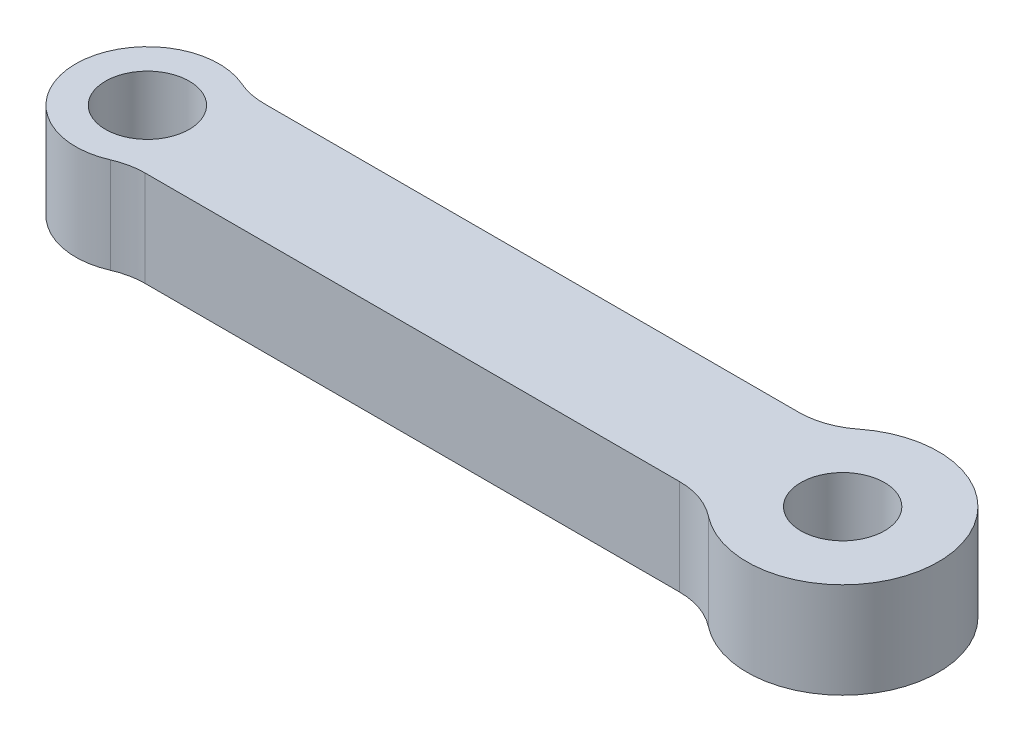
SolidWorks part; units mm, degrees
ref_plane "Ön Düzlem" through (0, 0, 0) normal (0, 0, 1) x (1, 0, 0)
ref_plane "Üst Düzlem" through (0, 0, 0) normal (0, 1, 0) x (1, 0, 0)
ref_plane "Sağ Düzlem" through (0, 0, 0) normal (1, 0, 0) x (0, 0, -1)
sketch "Çizim1" plane through (0, 0, 0) normal (0, 1, 0) x (1, 0, 0)
  line L0 (-55, 0) -> (55, 0) construction
  line L1 (-10.2187, -2.5) -> (4.0711, -2.5)
  line L2 (-10.2187, 2.5) -> (4.0711, 2.5)
  line L3 (-10.2187, 2.5) -> (-11.17, 2.5)
  line L4 (-10.2187, -2.5) -> (-11.17, -2.5)
  line L5 (4.0711, -2.5) -> (11.17, -2.5)
  line L6 (4.0711, 2.5) -> (11.17, 2.5)
  line L7 (0, -55) -> (0, 55) construction
  circle A0 centre (-13.5679, 0) radius 1.75
  arc A1 (-12.369, 2.75) -> (-12.369, -2.75) centre (-13.5679, 0) ccw
  circle A2 centre (15.5001, 0) radius 1.75
  arc A3 (13.0258, -3.1429) -> (13.0258, 3.1429) centre (15.5001, 0) ccw
  arc A4 (11.17, -2.5) -> (13.0258, -3.1429) centre (11.17, -5.5) cw
  arc A5 (11.17, 2.5) -> (13.0258, 3.1429) centre (11.17, 5.5) ccw
  arc A6 (-12.369, -2.75) -> (-11.17, -2.5) centre (-11.17, -5.5) cw
  arc A7 (-11.17, 2.5) -> (-12.369, 2.75) centre (-11.17, 5.5) cw
  dimension "D1" = 6
  dimension "D2" = 3.5
  dimension "D3" = 3.5
  dimension "D4" = 8
  dimension "D7" = 3
  dimension "D5" = 5
  dimension "D6" = 2.5
  dimension "D8" = 22.34
  dimension "D9" = 11.17
extrude "Yükseklik-Ekstrüzyon1" add sketch "Çizim1" along normal blind 4
